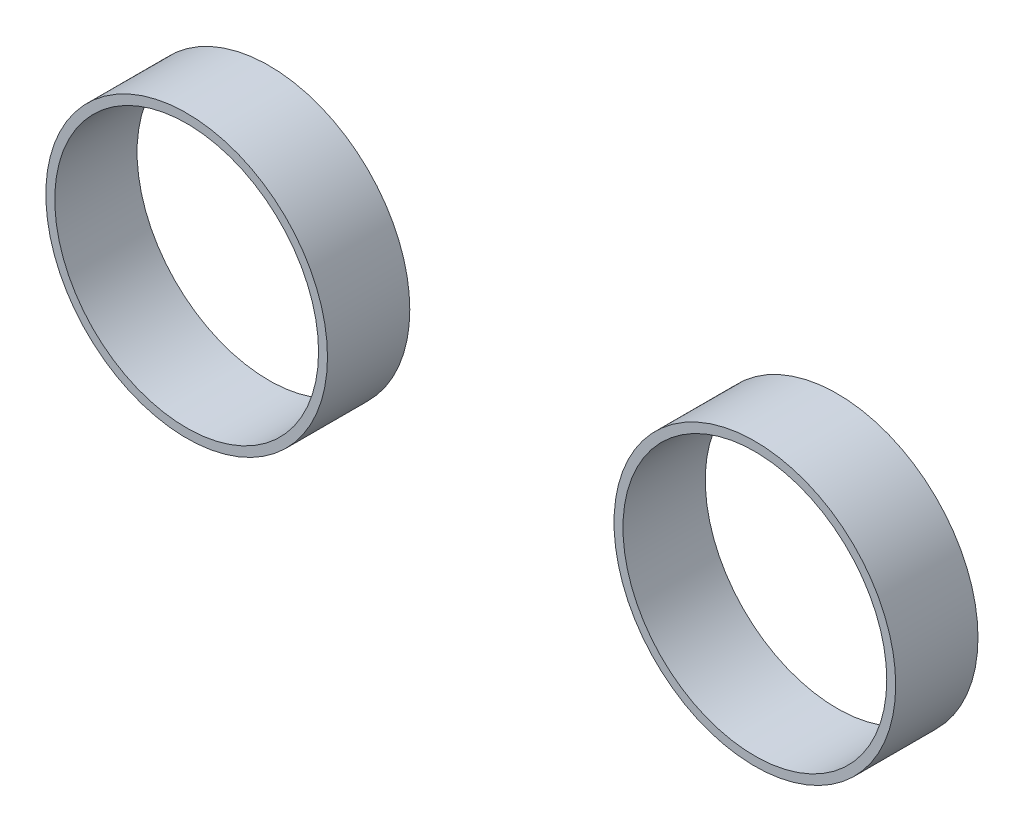
SolidWorks part; units mm, degrees
material "Velcro"
ref_plane "Front Plane" through (0, 0, 0) normal (0, 0, 1) x (1, 0, 0)
ref_plane "Top Plane" through (0, 0, 0) normal (0, 1, 0) x (1, 0, 0)
ref_plane "Right Plane" through (0, 0, 0) normal (1, 0, 0) x (0, 0, -1)
sketch "Sketch1" plane through (0, 0, 0) normal (0, 0, 1) x (1, 0, 0)
  circle A0 centre (1435.9805, -423.3823) radius 65
  circle A1 centre (1435.9805, -423.3823) radius 69.4
  circle A2 centre (1715.9805, -423.3823) radius 65
  circle A3 centre (1715.9805, -423.3823) radius 69.4
  dimension "D1" = 130
  dimension "D3" = 130
  dimension "D4" = 4.4
  dimension "D2" = 4.4
extrude "Boss-Extrude1" add sketch "Sketch1" along normal blind 40.56
